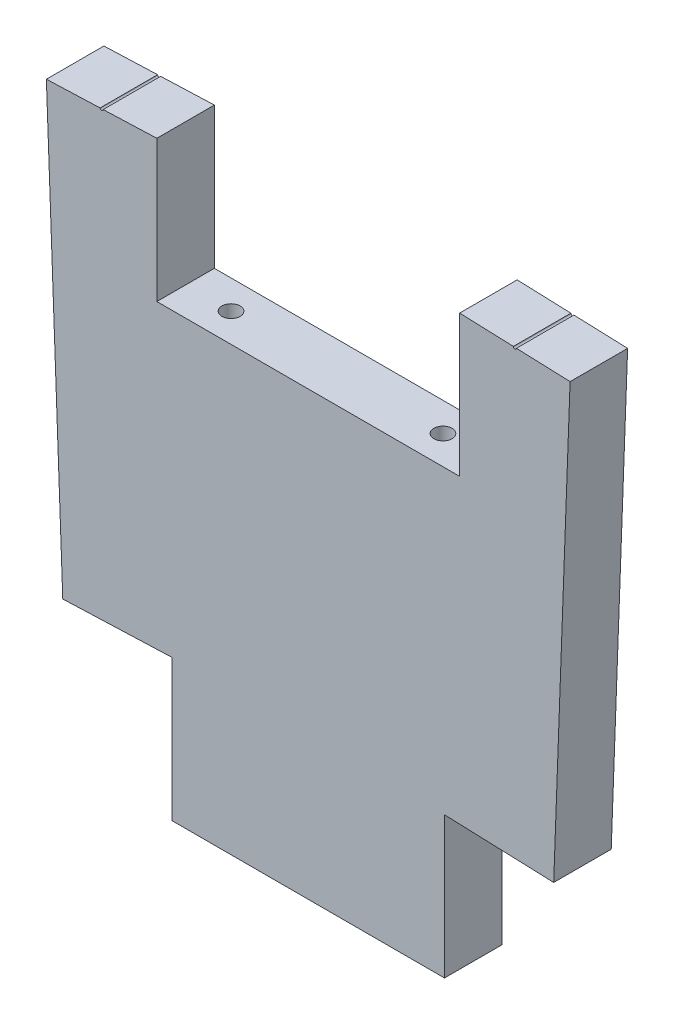
SolidWorks part; units mm, degrees
ref_plane "Front Plane" through (0, 0, 0) normal (0, 0, 1) x (1, 0, 0)
ref_plane "Top Plane" through (0, 0, 0) normal (0, 1, 0) x (1, 0, 0)
ref_plane "Right Plane" through (0, 0, 0) normal (1, 0, 0) x (0, 0, -1)
sketch "Sketch1" plane through (0, 0, 0) normal (0, 0, 1) x (1, 0, 0)
  line L0 (0, 0) -> (70.7413, 283.4044)
  line L1 (86.489, 32.6481) -> (2523.2123, -57.7618)
  line L2 (2523.2123, -57.7618) -> (2519.4304, -159.6916)
  line L3 (2519.4304, -159.6916) -> (82.707, -69.2817)
  line L4 (82.707, -69.2817) -> (86.489, 32.6481)
  line L5 (2519.4304, -159.6916) -> (120.707, -159.6916) construction
  line L6 (82.707, -70.6916) -> (120.707, -70.6916)
  line L7 (82.707, -70.6916) -> (82.707, -159.6916)
  line L8 (82.707, -159.6916) -> (120.707, -159.6916)
  line L9 (120.707, -70.6916) -> (120.707, -159.6916)
  line L10 (12.0114, 48.1202) -> (111.9426, 44.4125)
  line L11 (-50, 0) -> (50, 0)
  line L12 (-50, 0) -> (-50, -12.7)
  line L13 (-50, -12.7) -> (50, -12.7)
  line L14 (50, 0) -> (50, -12.7)
  line L15 (111.9426, 44.4125) -> (111.4718, 31.7212)
  line L16 (111.4718, 31.7212) -> (11.5405, 35.429)
  line L17 (11.5405, 35.429) -> (12.0114, 48.1202)
  line L18 (2523.2123, 142.3758) -> (0, 235.9948) construction
  line L19 (58.3667, 233.8292) -> (732.0562, -93.3746) construction
  line L20 (74.2991, 249.1801) -> (58.3667, 233.8292)
  line L21 (58.3667, 233.8292) -> (58.3667, 20.4846) construction
  line L22 (0, 0) -> (0, -236.7459) construction
  line L23 (-2519.4304, -159.6916) -> (-120.707, -159.6916) construction
  line L26 (-120.707, -70.6916) -> (-120.707, -159.6916)
  line L27 (-82.707, -159.6916) -> (-120.707, -159.6916)
  line L28 (-82.707, -70.6916) -> (-82.707, -159.6916)
  line L29 (-82.707, -70.6916) -> (-120.707, -70.6916)
  line L30 (-82.707, -69.2817) -> (-86.489, 32.6481)
  line L31 (-2519.4304, -159.6916) -> (-82.707, -69.2817)
  line L32 (-2523.2123, -57.7618) -> (-2519.4304, -159.6916)
  line L33 (-86.489, 32.6481) -> (-2523.2123, -57.7618)
  point P15 (0, 0)
  dimension "D1" = 292.1
  dimension "D2" = 2438.4
  dimension "D3" = 102
  dimension "D4" = 38
  dimension "D5" = 89
  dimension "D6" = 12.7
  dimension "D7" = 100
  dimension "D8" = 200
  dimension "D9" = 78.11
  dimension "D10" = 78.11
  dimension "D11" = 50
  dimension "D12" = 100
  dimension "D13" = 25
  dimension "D14" = 46.06
  dimension "D15" = 46.065
  dimension "D16" = 32.05
sketch "Sketch2" plane through (0, 0, 0) normal (0, 0, 1) x (1, 0, 0)
  line L0 (-50, -12.7) -> (50, -12.7)
  line L1 (-50, -12.7) -> (50, -12.7) construction
  line L2 (50, -12.7) -> (50, 34.002)
  line L3 (111.4718, 31.7212) -> (11.5405, 35.429) construction
  line L4 (50, 34.002) -> (86.489, 32.6481)
  line L5 (86.489, 32.6481) -> (79.3897, -158.6916)
  line L6 (79.3897, -158.6916) -> (-79.3897, -158.6916)
  line L7 (0, -158.6916) -> (0, -12.7) construction
  line L8 (82.707, -159.6916) -> (120.707, -159.6916) construction
  line L9 (-86.489, 32.6481) -> (-79.3897, -158.6916)
  line L10 (-50, 34.002) -> (-86.489, 32.6481)
  line L11 (-50, -12.7) -> (-50, 34.002)
  dimension "D1" = 1
extrude "Boss-Extrude1" add sketch "Sketch2" against normal blind 19
sketch "Sketch4" plane through (0, 0, -19) normal (0, 0, -1) x (-1, 0, 0)
  line L0 (177, -116.8873) -> (45, -111.9897)
  line L1 (45, -111.9897) -> (45, -158.6916)
  line L2 (45, -158.6916) -> (-45, -158.6916)
  line L3 (-45, -158.6916) -> (-45, -111.9897)
  line L4 (-45, -111.9897) -> (-160.8148, -116.2867)
  line L5 (-160.8148, -116.2867) -> (-160.8148, -226.3289)
  line L6 (-160.8148, -226.3289) -> (177, -226.3289)
  line L7 (177, -226.3289) -> (177, -116.8873)
  line L8 (50, -12.7) -> (50, 34.002) construction
  line L9 (-50, 34.002) -> (-50, -12.7) construction
  line L10 (-111.4718, 31.7212) -> (-11.5405, 35.429) construction
  line L11 (50, 34.002) -> (86.489, 32.6481) construction
  line L12 (79.3897, -158.6916) -> (-79.3897, -158.6916) construction
  line L13 (0, 0) -> (0, -198.7369) construction
  line L14 (-50, 34.002) -> (-50, -12.7) construction
  line L15 (50, -12.7) -> (50, 34.002) construction
  dimension "D1" = 5
  dimension "D2" = 5
extrude "Cut-Extrude1" cut sketch "Sketch4" against normal blind 19
sketch "Sketch5" plane through (0, 0, 0) normal (0, 0, 1) x (1, 0, 0)
  line L0 (81.1882, 51.6055) -> (79.8951, 16.7543) construction
  line L1 (56.6423, 51.2016) -> (55.5023, 20.4756) construction
  line L2 (111.9426, 44.4125) -> (111.4718, 31.7212) construction
  dimension "D1" = 6
  dimension "D2" = 6
  dimension "D3" = 24.5141
  dimension "D4" = 31
sketch "Sketch6" plane through (0, -12.7, 0) normal (0, 1, 0) x (1, 0, 0)
  circle A0 centre (35, 9.5) radius 3
  circle A1 centre (-35, 9.5) radius 3
  dimension "D1" = 6
  dimension "D2" = 6
extrude "Cut-Extrude2" cut sketch "Sketch6" against normal blind 10
sketch "Sketch7" plane through (0, 0, -19) normal (0, 0, -1) x (-1, 0, 0)
  line L0 (50, 34.002) -> (86.489, 32.6481) construction
  line L1 (0, 0) -> (0, 41.0873) construction
  circle A0 centre (68.2445, 33.3251) radius 0.5
  circle A1 centre (-68.2445, 33.3251) radius 0.5
  point P4 (68.2445, 33.3251)
  dimension "D1" = 1
extrude "Cut-Extrude3" cut sketch "Sketch7" against normal blind 20
